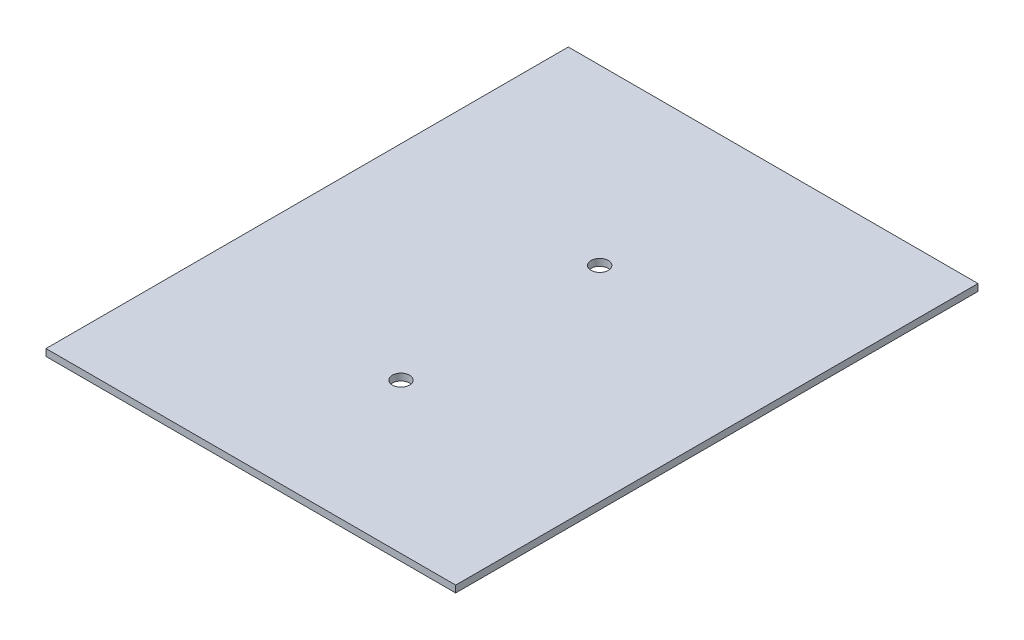
SolidWorks part; units mm, degrees
ref_plane "Front Plane" through (0, 0, 0) normal (0, 0, 1) x (1, 0, 0)
ref_plane "Top Plane" through (0, 0, 0) normal (0, 1, 0) x (1, 0, 0)
ref_plane "Right Plane" through (0, 0, 0) normal (1, 0, 0) x (0, 0, -1)
sketch "Sketch1" plane through (0, 0, 0) normal (0, 1, 0) x (1, 0, 0)
  line L1 (-35.7607, 145.5685) -> (202.3365, 145.5685)
  line L2 (-35.7607, 145.5685) -> (-35.7607, -157.9889)
  line L3 (-35.7607, -157.9889) -> (202.3365, -157.9889)
  line L4 (202.3365, 145.5685) -> (202.3365, -157.9889)
  circle A0 centre (83.2879, 44.7356) radius 5
  circle A1 centre (83.2879, -70.7344) radius 5
  point P8 (0, 0)
  point P9 (0, 0)
  point P11 (83.2879, -157.9889)
extrude "Boss-Extrude1" add sketch "Sketch1" along normal blind 4
equation "\"b\"=100"
equation "\"p\"=5"
equation "\"D2@Sketch1\"=\"p\""
equation "\"c\"= \"b\" / cos ( 180 / 6 )"
equation "\"D4@Sketch1\"=\"b\"/cos(180/6)"
equation "\"D6@Sketch1\"=\"b\""
equation "\"a\"= ( \"c\" ^ 2 - \"b\" ^ 2 ) ^ .5"
equation "\"s\"= \"a\" + \"b\" - \"c\""
equation "\"y\"= \"a\" - ( \"p\" * 1.5 )"
equation "\"D5@Sketch1\"=\"s\""
equation "\"D7@Sketch1\"=\"y\"*2"
equation "\"D13@Sketch1\"=\"p\"*2"
equation "\"D1@Sketch1\"=\"c\""
